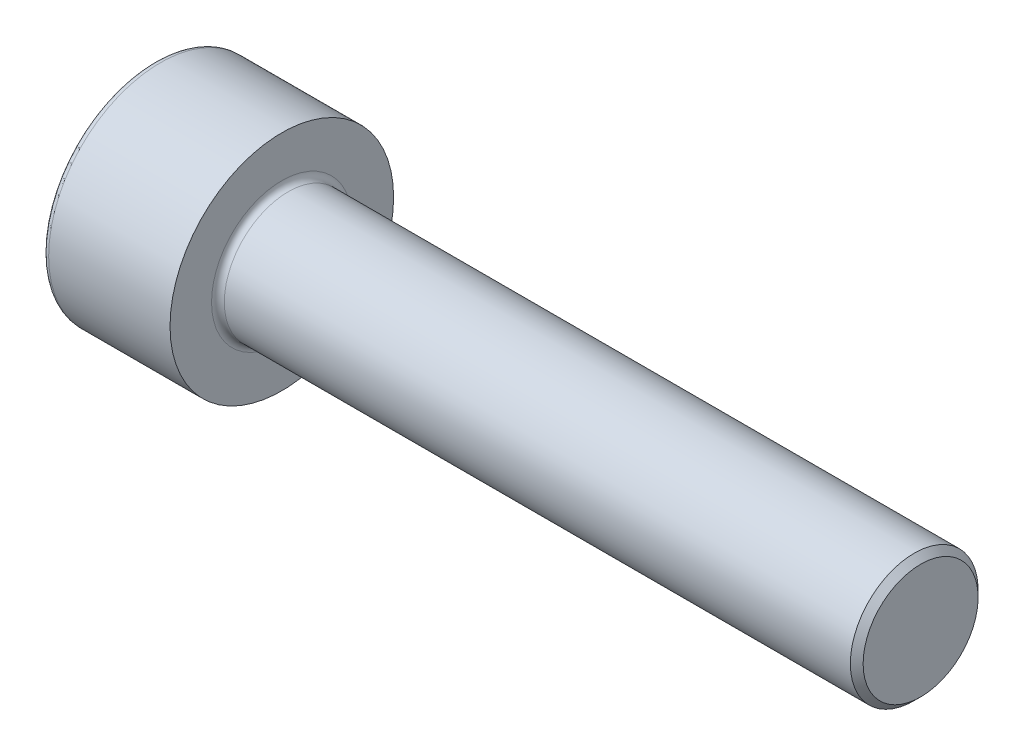
SolidWorks part; units mm, degrees
material "Q235-A"
ref_plane "Front Plane" through (0, 0, 0) normal (0, 0, 1) x (1, 0, 0)
ref_plane "Top Plane" through (0, 0, 0) normal (0, 1, 0) x (1, 0, 0)
ref_plane "Right Plane" through (0, 0, 0) normal (1, 0, 0) x (0, 0, -1)
sketch "草图1" plane through (0, 0, 0) normal (0, 0, 1) x (1, 0, 0)
  line L0 (0, 0) -> (21.833, 0) construction
  line L1 (0, 0) -> (0, 3.5)
  line L2 (0, 3.5) -> (4, 3.5)
  line L3 (4, 3.5) -> (4, 2)
  line L4 (4, 2) -> (24, 2)
  line L5 (24, 2) -> (24, 0)
  line L6 (24, 0) -> (0, 0)
  dimension "D1" = 4
  dimension "D2" = 7
  dimension "D3" = 4
  dimension "D4" = 20
revolve "旋转1" add sketch "草图1" angle 360 about L0
hole_wizard "Ø3.0 (3) 直径孔1" positions "草图4" profile "草图3" hole size "Ø3.0" standard "GB"
sketch "草图4" plane through (0, 0, 0) normal (-1, 0, 0) x (0, 0, 1)
  point P0 (0, 0)
sketch "草图3" plane through (0, 0, 0) normal (0, 1, 0) x (0, 0, 1)
  line L0 (0, 0) -> (0, 3.5013)
  line L1 (0, 3.5013) -> (1.5, 2.6)
  line L2 (1.5, 2.6) -> (1.5, 0)
  line L5 (1.5, 0) -> (0, 0)
  line L10 (0, 3.5013) -> (-1.5, 2.6) construction
  line L11 (0, -6.35) -> (0, 107.95) construction
  dimension "孔直径" = 3
  dimension "孔深度" = 2.6
  dimension "导头角度" = 118
sketch "草图2" plane through (0, 0, 0) normal (-1, 0, 0) x (0, 0, 1)
  line L1 (0.866, 1.5) -> (-0.866, 1.5)
  line L2 (-0.866, 1.5) -> (-1.7321, 0)
  line L3 (-1.7321, 0) -> (-0.866, -1.5)
  line L4 (-0.866, -1.5) -> (0.866, -1.5)
  line L5 (0.866, -1.5) -> (1.7321, 0)
  line L6 (1.7321, 0) -> (0.866, 1.5)
  circle A0 centre (0, 0) radius 1.5 construction
  dimension "D1" = 3
extrude "切除-拉伸1" cut sketch "草图2" against normal offset from surface (2.6 mm away) 1.4 up to face at (4, 0, 3.5)
fillet "圆角1" radius 0.2 2 edges at (0, 0, 3.5) (4, 0, 2)
chamfer "倒角1" distance 0.2 angle 45 1 edges at (24, 0, 2)
